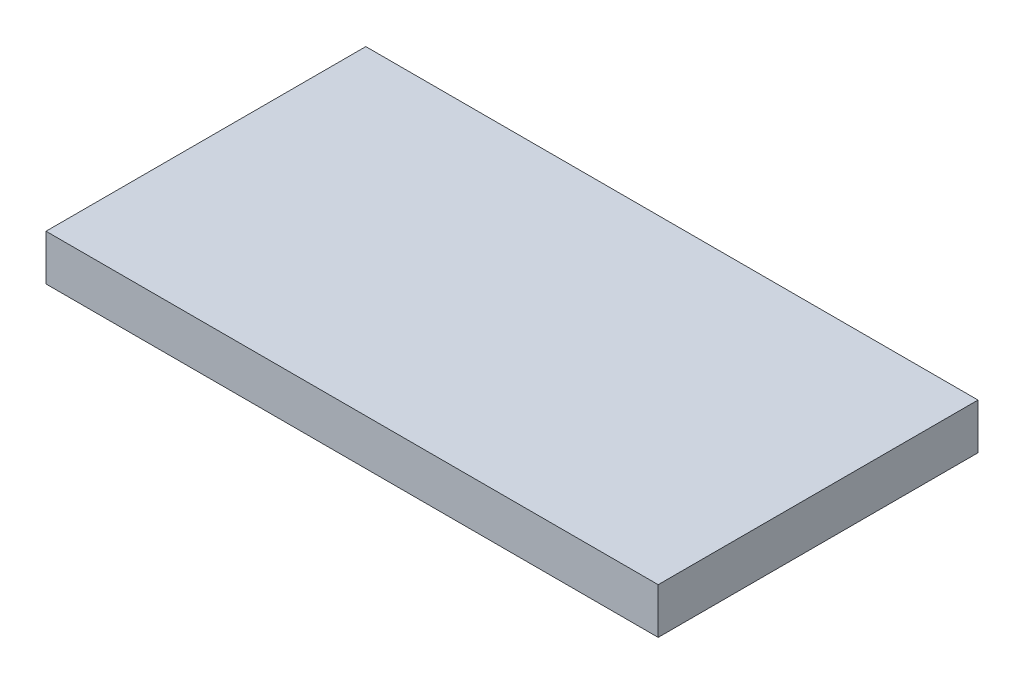
SolidWorks part; units mm, degrees
ref_plane "Alzado" through (0, 0, 0) normal (0, 0, 1) x (1, 0, 0)
ref_plane "Planta" through (0, 0, 0) normal (0, 1, 0) x (1, 0, 0)
ref_plane "Vista lateral" through (0, 0, 0) normal (1, 0, 0) x (0, 0, -1)
sketch "Croquis1" plane through (0, 0, 0) normal (0, 1, 0) x (1, 0, 0)
  line L1 (0, 0) -> (134, 0)
  line L2 (0, 0) -> (0, 70)
  line L3 (0, 70) -> (134, 70)
  line L4 (134, 0) -> (134, 70)
  dimension "D1" = 134
  dimension "D2" = 70
extrude "Saliente-Extruir1" add sketch "Croquis1" along normal blind 10
